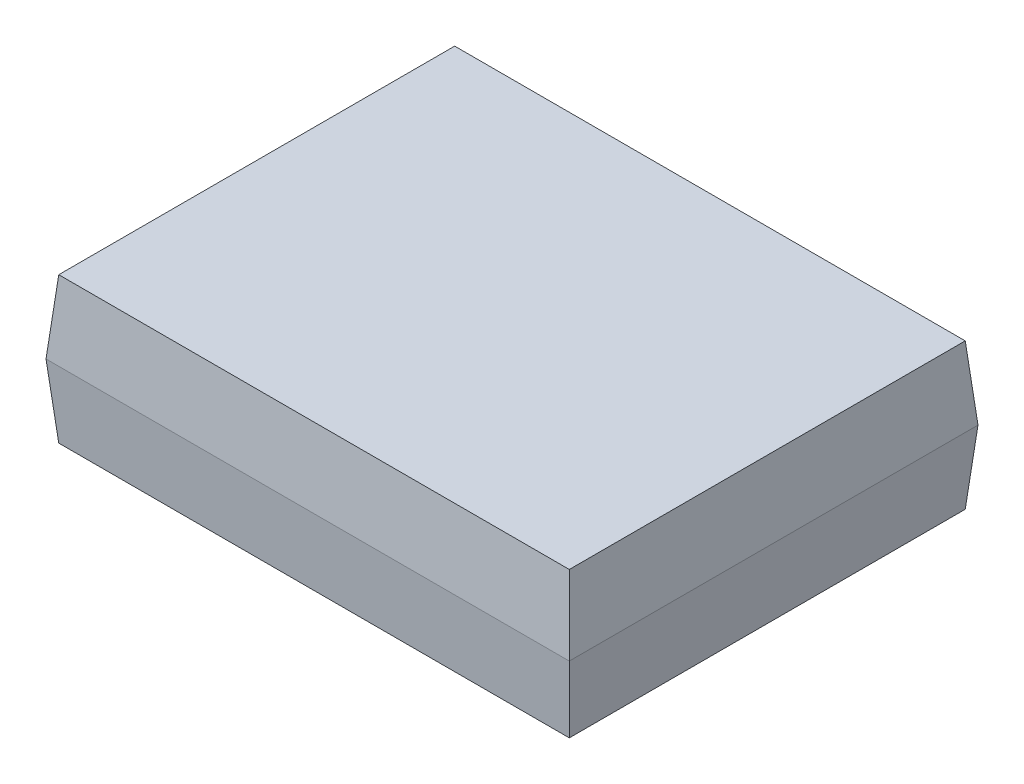
SolidWorks part; units mm, degrees
ref_plane "Plan de face" through (0, 0, 0) normal (0, 0, 1) x (1, 0, 0)
ref_plane "Plan de dessus" through (0, 0, 0) normal (0, 1, 0) x (1, 0, 0)
ref_plane "Plan de droite" through (0, 0, 0) normal (1, 0, 0) x (0, 0, -1)
sketch "Esquisse1" plane through (0, 0, 0) normal (0, 1, 0) x (1, 0, 0)
  line L1 (0, 0) -> (4.9, 0)
  line L2 (0, 0) -> (0, 3.8)
  line L3 (0, 3.8) -> (4.9, 3.8)
  line L4 (4.9, 0) -> (4.9, 3.8)
  dimension "D1" = 4.9
  dimension "D2" = 3.8
extrude "Boss.-Extru.1" add sketch "Esquisse1" along normal blind 0.7 draft 5 draft outward yes
sketch "Esquisse2" plane through (0, 0.7, 0) normal (0, 1, 0) x (1, 0, 0)
  line L1 (-0.0612, 3.8612) -> (4.9612, 3.8612)
  line L2 (-0.0612, 3.8612) -> (-0.0612, -0.0612)
  line L3 (-0.0612, -0.0612) -> (4.9612, -0.0612)
  line L4 (4.9612, 3.8612) -> (4.9612, -0.0612)
extrude "Boss.-Extru.2" add sketch "Esquisse2" along normal blind 0.7 draft 5
ref_plane "Plan1" through (0, 0, -1.9) normal (0, 0, 1) x (1, 0, 0)
